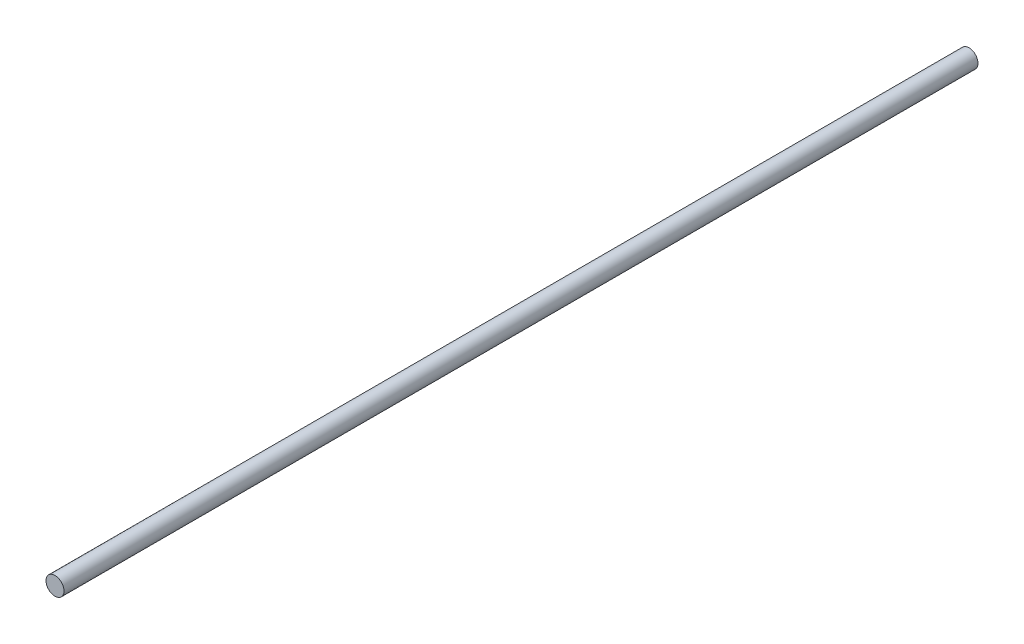
SolidWorks part; units mm, degrees
material "Plain Carbon Steel"
ref_plane "Front Plane" through (0, 0, 0) normal (0, 0, 1) x (1, 0, 0)
ref_plane "Top Plane" through (0, 0, 0) normal (0, 1, 0) x (1, 0, 0)
ref_plane "Right Plane" through (0, 0, 0) normal (1, 0, 0) x (0, 0, -1)
sketch "Sketch1" plane through (0, 0, 0) normal (0, 0, 1) x (1, 0, 0)
  circle A0 centre (6.9996, 4.8031) radius 4
  dimension "D1" = 8
extrude "Boss-Extrude1" add sketch "Sketch1" against normal blind 406
